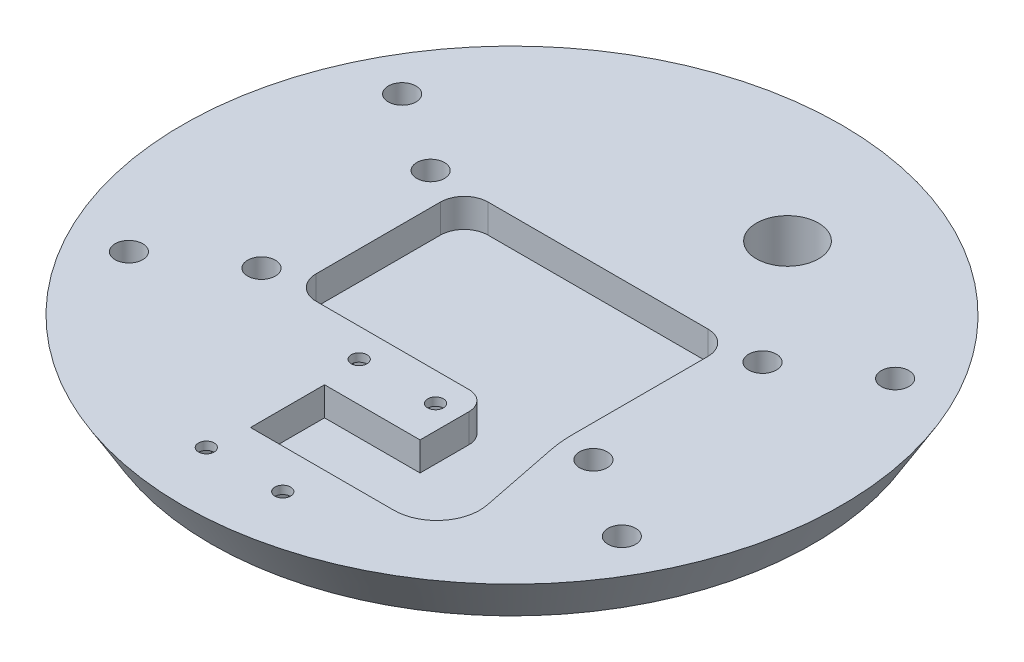
SolidWorks part; units mm, degrees
ref_plane "Front Plane" through (0, 0, 0) normal (0, 0, 1) x (1, 0, 0)
ref_plane "Top Plane" through (0, 0, 0) normal (0, 1, 0) x (1, 0, 0)
ref_plane "Right Plane" through (0, 0, 0) normal (1, 0, 0) x (0, 0, -1)
sketch "Sketch1" plane through (0, 0, 0) normal (0, 0, 1) x (1, 0, 0)
  line L0 (0, 0) -> (63, 0)
  line L1 (63, 0) -> (69, 10)
  line L8 (69, 10) -> (0, 10)
  line L10 (0, 10) -> (0, 0)
  dimension "D1" = 69
  dimension "D2" = 63
  dimension "D3" = 10
revolve "Revolve1" add sketch "Sketch1" angle 360 about L10
sketch "Sketch4" plane through (0, 0, 0) normal (0, 1, 0) x (1, 0, 0)
  line L0 (-63, 0) -> (63, 0) construction
  line L1 (0, 63) -> (0, -63) construction
  line L2 (0, 0) -> (34.7493, 17.7056) construction
  line L3 (0, 0) -> (51.6026, 28.6038) construction
  circle A1 centre (34.7493, 17.7056) radius 1.65
  circle A2 centre (51.6026, 28.6038) radius 1.65
  circle A4 centre (51.6026, -28.6038) radius 1.65
  circle A5 centre (34.7493, -17.7056) radius 1.65
  circle A6 centre (-34.7493, -17.7056) radius 1.65
  circle A7 centre (-51.6026, -28.6038) radius 1.65
  circle A8 centre (-51.6026, 28.6038) radius 1.65
  circle A9 centre (-34.7493, 17.7056) radius 1.65
  circle A10 centre (0, 0) radius 63 construction
  point P2 (0, 0)
  point P3 (0, 0)
  point P26 (0, 0)
  point P27 (0, 0)
  point P28 (0, 0)
  dimension "D5" = 3.3
  dimension "D6" = 3.3
  dimension "D7" = 126
  dimension "D1" = 27
  dimension "D2" = 29
  dimension "D3" = 39
  dimension "D4" = 59
extrude "Cut-Extrude1" cut sketch "Sketch4" along normal blind 4
sketch "Sketch5" plane through (0, 0, 0) normal (0, -1, 0) x (-1, 0, 0)
  circle A0 centre (-51.6026, 28.6038) radius 2.9
  circle A1 centre (-51.6026, -28.6038) radius 2.9
  circle A2 centre (51.6026, -28.6038) radius 2.9
  circle A3 centre (51.6026, 28.6038) radius 2.9
  circle A4 centre (-34.7493, 17.7056) radius 2.9
  circle A5 centre (-34.7493, -17.7056) radius 2.9
  circle A6 centre (34.7493, -17.7056) radius 2.9
  circle A7 centre (34.7493, 17.7056) radius 2.9
  dimension "D1" = 5.8
extrude "Cut-Extrude2" cut sketch "Sketch5" along direction (0, 1, 0) on the side against the normal through all from offset 4
sketch "Sketch7" plane through (0, 0, 0) normal (0, -1, 0) x (-1, 0, 0)
  line L0 (0, 0) -> (-15.3909, 42.2862) construction
  line L1 (0, 0) -> (0, 50000) construction
  circle A0 centre (-15.3909, 42.2862) radius 6.5
  dimension "D1" = 13
  dimension "D2" = 20
  dimension "D3" = 45
extrude "Cut-Extrude4" cut sketch "Sketch7" against normal blind 10
sketch "Sketch10" plane through (0, 10, 0) normal (0, 1, 0) x (-1, 0, 0)
  line L1 (-8, 56) -> (8, 56) construction
  line L2 (-8, 56) -> (-8, 24) construction
  line L3 (-8, 24) -> (8, 24) construction
  line L4 (8, 56) -> (8, 24) construction
  line L5 (-13, 32.25) -> (7, 32.25)
  line L7 (-23, 47.75) -> (7, 47.75)
  line L8 (7, 32.25) -> (7, 47.75)
  line L12 (-23, -18) -> (23, -18)
  line L13 (28, -13) -> (28, 13)
  line L14 (23, 18) -> (-9, 18)
  line L15 (-13, 22) -> (-13, 32.25)
  line L16 (-31.8248, 36.9828) -> (-28.4867, 20.3137)
  line L17 (-28, 15.4048) -> (-28, -13)
  line L18 (-28, 0) -> (28, 0) construction
  circle A0 centre (-8, 56) radius 1.65
  circle A1 centre (8, 56) radius 1.65
  circle A2 centre (8, 24) radius 1.65
  circle A3 centre (-8, 24) radius 1.65
  arc A4 (-23, 47.75) -> (-31.8248, 36.9828) centre (-23, 38.75) ccw
  arc A5 (-28.4867, 20.3137) -> (-28, 15.4048) centre (-53, 15.4048) cw
  arc A6 (-9, 18) -> (-13, 22) centre (-9, 22) cw
  arc A8 (-23, -18) -> (-28, -13) centre (-23, -13) cw
  arc A9 (23, -18) -> (28, -13) centre (23, -13) ccw
  arc A10 (28, 13) -> (23, 18) centre (23, 13) ccw
  point P4 (-12.4026, 32.25)
  point P5 (0, 0)
  point P6 (0, 24)
  point P18 (7, 40)
  point P19 (-13, 32.25)
  point P30 (-15, 32.25)
  point P31 (-14.7995, 32.25)
  point P48 (8, 40)
  dimension "D4" = 3.3
  dimension "D8" = 4
  dimension "D9" = 5
  dimension "D14" = 9
  dimension "D15" = 25
  dimension "D1" = 16
  dimension "D2" = 32
  dimension "D3" = 24
  dimension "D5" = 7
  dimension "D6" = 15.5
  dimension "D7" = 30
  dimension "D10" = 18
  dimension "D11" = 18
  dimension "D12" = 20
  dimension "D16" = 56
  dimension "D17" = 17
extrude "Cut-Extrude5" cut sketch "Sketch10" against normal blind 6
sketch "Sketch11" plane through (0, 10, 0) normal (0, 1, 0) x (-1, 0, 0)
  line L1 (-4.6514, 56) -> (-6.3257, 58.9)
  line L2 (-6.3257, 58.9) -> (-9.6743, 58.9)
  line L3 (-9.6743, 58.9) -> (-11.3486, 56)
  line L4 (-11.3486, 56) -> (-9.6743, 53.1)
  line L5 (-9.6743, 53.1) -> (-6.3257, 53.1)
  line L6 (-6.3257, 53.1) -> (-4.6514, 56)
  line L7 (11.3476, 56.0843) -> (9.6008, 58.9412)
  line L8 (9.6008, 58.9412) -> (6.2532, 58.8569)
  line L9 (6.2532, 58.8569) -> (4.6524, 55.9157)
  line L10 (4.6524, 55.9157) -> (6.3992, 53.0588)
  line L11 (6.3992, 53.0588) -> (9.7468, 53.1431)
  line L12 (9.7468, 53.1431) -> (11.3476, 56.0843)
  line L13 (-5.1, 25.6743) -> (-8, 27.3486)
  line L14 (-8, 27.3486) -> (-10.9, 25.6743)
  line L15 (-10.9, 25.6743) -> (-10.9, 22.3257)
  line L16 (-10.9, 22.3257) -> (-8, 20.6514)
  line L17 (-8, 20.6514) -> (-5.1, 22.3257)
  line L18 (-5.1, 22.3257) -> (-5.1, 25.6743)
  line L19 (10.8989, 22.3238) -> (10.9011, 25.6725)
  line L20 (10.9011, 25.6725) -> (8.0022, 27.3486)
  line L21 (8.0022, 27.3486) -> (5.1011, 25.6762)
  line L22 (5.1011, 25.6762) -> (5.0989, 22.3275)
  line L23 (5.0989, 22.3275) -> (7.9978, 20.6514)
  line L24 (7.9978, 20.6514) -> (10.8989, 22.3238)
  circle A0 centre (-8, 56) radius 2.9 construction
  circle A1 centre (8, 56) radius 2.9 construction
  circle A2 centre (-8, 24) radius 2.9 construction
  circle A3 centre (8, 24) radius 2.9 construction
  circle A4 centre (-8, 24) radius 1.65 construction
  circle A5 centre (8, 24) radius 1.65 construction
  point P28 (-8, 27.3486)
  point P37 (-17.5003, 21.1)
  point P38 (-7.6874, 23.5446)
  point P41 (0, 0)
  point P42 (8.285, 26.0627)
  dimension "D1" = 5.8
extrude "Cut-Extrude6" cut sketch "Sketch11" against normal blind 2.6 from offset 1.7
